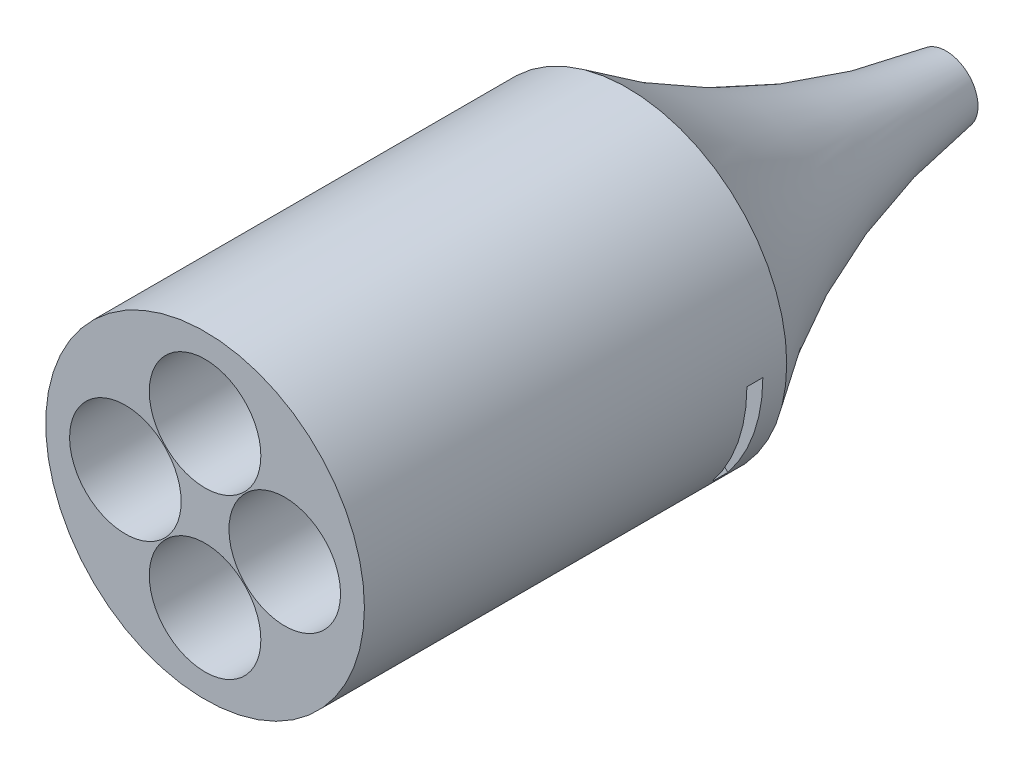
SolidWorks part; units mm, degrees
ref_plane "Alzado" through (0, 0, 0) normal (0, 0, 1) x (1, 0, 0)
ref_plane "Planta" through (0, 0, 0) normal (0, 1, 0) x (1, 0, 0)
ref_plane "Vista lateral" through (0, 0, 0) normal (1, 0, 0) x (0, 0, -1)
sketch "Croquis1" plane through (0, 0, 0) normal (0, 0, 1) x (1, 0, 0)
  circle A0 centre (-44.2113, 7.2973) radius 20
extrude "Saliente-Extruir1" add sketch "Croquis1" along normal blind 3
sketch "Croquis2" plane through (0, 0, 3) normal (0, 0, 1) x (1, 0, 0)
  line L1 (-64.2113, 7.2973) -> (-24.2113, 7.2973) construction
  line L2 (-44.2113, 7.2973) -> (-44.2113, 27.2973) construction
  circle A0 centre (-44.2113, 7.2973) radius 20
  circle A2 centre (-44.2113, 17.2973) radius 7
  circle A3 centre (-34.2113, 7.2973) radius 7
  circle A4 centre (-44.2113, -2.7027) radius 7
  circle A5 centre (-54.2113, 7.2973) radius 7
  point P17 (-44.2113, 7.2973)
  dimension "D1" = 4
extrude "Saliente-Extruir2" add sketch "Croquis2" along normal blind 50
sketch "Croquis3" plane through (0, 0, 0) normal (0, 0, -1) x (-1, 0, 0)
  line L0 (64.2113, 7.2973) -> (24.2113, 7.2973) construction
  circle A0 centre (44.2113, 7.2973) radius 20 construction
ref_plane "Plano1" through (0, 7.2973, 0) normal (0, 1, 0) x (1, 0, 0)
sketch "Croquis4" plane through (0, 7.2973, 0) normal (0, 1, 0) x (1, 0, 0)
  line L0 (-44.2113, 0) -> (-48.2113, 0) construction
  line L1 (-64.2113, 0) -> (-24.2113, 0) construction
  line L2 (-48.2113, 0) -> (-64.2113, 0)
  line L3 (-48.2113, 0) -> (-48.2113, 40)
  line L4 (-44.2113, 0) -> (-44.2113, 30.3503) construction
  arc A0 (-48.2113, 40) -> (-64.2113, 0) centre (-133.8662, 51.062) cw
  dimension "D1" = 4
revolve "Revolución1" add sketch "Croquis4" angle 360 about L4
sketch "Croquis5" plane through (0, 0, 53) normal (0, 0, 1) x (1, 0, 0)
  line L0 (-44.2113, 7.2973) -> (-29.9286, -6.7028) construction
  line L1 (-29.9286, -6.7028) -> (-13.1087, 10.4565) construction
  circle A0 centre (-44.2113, 7.2973) radius 20 construction
ref_plane "Plano2" through (-11.9126, 11.6769, 0) normal (0.7141, -0.7, 0) x (0, 0, -1)
sketch "Croquis6" plane through (-11.9126, 11.6769, 0) normal (0.7141, -0.7, 0) x (0, 0, -1)
  line L0 (-53, -25.7369) -> (-3, -25.7369) construction
  line L6 (-3, -25.7369) -> (-3, -23.7369) construction
  line L7 (-3, -25.7369) -> (-3, -27.7369) construction
  line L8 (-3, -23.7369) -> (-5, -23.7369)
  line L9 (-3, -23.7369) -> (-3, -11.7369)
  line L11 (-5, -23.7369) -> (-5, -11.7369)
  line L12 (-5, -11.7369) -> (-3, -11.7369)
  line L13 (-3, -27.7369) -> (-5, -27.7369)
  line L14 (-3, -27.7369) -> (-3, -39.7369)
  line L15 (-3, -39.7369) -> (-5, -39.7369)
  line L16 (-5, -27.7369) -> (-5, -39.7369)
  dimension "D1" = 28
  dimension "D2" = 2
  dimension "D3" = 50
extrude "Cortar-Extruir1" cut sketch "Croquis6" against normal blind 32
